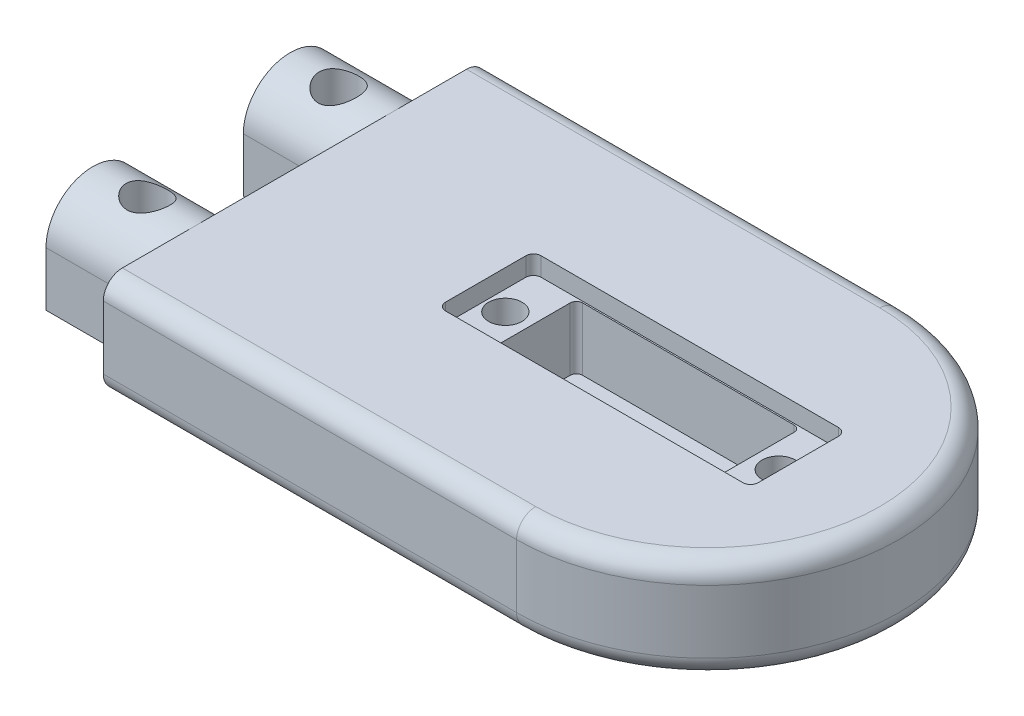
SolidWorks part; units mm, degrees
ref_plane "Front Plane" through (0, 0, 0) normal (0, 0, 1) x (1, 0, 0)
ref_plane "Top Plane" through (0, 0, 0) normal (0, 1, 0) x (1, 0, 0)
ref_plane "Right Plane" through (0, 0, 0) normal (1, 0, 0) x (0, 0, -1)
sketch "Sketch1" plane through (0, 0, 0) normal (1, 0, 0) x (0, 0, -1)
  line L0 (-20, -5.305) -> (20, -5.305)
  line L1 (-20, -5.305) -> (-20, 5.305)
  line L2 (-20, 5.305) -> (20, 5.305)
  line L3 (20, -5.305) -> (20, 5.305)
  line L4 (-20, 5.305) -> (20, -5.305) construction
  line L5 (-20, -5.305) -> (20, 5.305) construction
  point P5 (0, 0)
  dimension "D1" = 40
  dimension "D2" = 10.61
extrude "Boss-Extrude1" add sketch "Sketch1" along normal blind 63.235
sketch "Sketch2" plane through (0, 5.305, 0) normal (0, 1, 0) x (1, 0, 0)
  line L0 (63.235, -20) -> (63.235, 0)
  line L1 (63.235, 20) -> (63.235, -20) construction
  line L2 (63.235, -20) -> (43.235, -20)
  line L3 (63.235, -20) -> (0, -20) construction
  arc A0 (43.235, -20) -> (63.235, 0) centre (43.235, 0) ccw
extrude "Cut-Extrude1" cut sketch "Sketch2" against normal through all
ref_plane "Plane1" through (0, 0, 0) normal (0, 0, 1) x (1, 0, 0)
mirror "Mirror1" about plane through (0, 0, 0) normal (0, 0, 1) of "Cut-Extrude1"
sketch "Sketch3" plane through (0, 5.305, 0) normal (0, 1, 0) x (1, 0, 0)
  line L0 (20, 4.2) -> (20, -4.2)
  line L1 (51.91, 5) -> (41.54, 5)
  line L2 (52.71, -4.2) -> (52.71, 4.2)
  line L3 (41.54, -5) -> (51.91, -5)
  line L4 (31.17, -5) -> (41.54, -5)
  line L5 (41.54, 5) -> (31.17, 5)
  line L6 (31.17, 5) -> (20.8, 5)
  line L7 (20.8, -5) -> (31.17, -5)
  line L8 (43.235, 20) -> (0, 20) construction
  line L9 (0, 20) -> (0, -20) construction
  arc A0 (52.71, 4.2) -> (51.91, 5) centre (51.91, 4.2) ccw
  arc A1 (51.91, -5) -> (52.71, -4.2) centre (51.91, -4.2) ccw
  arc A2 (20.8, 5) -> (20, 4.2) centre (20.8, 4.2) ccw
  arc A3 (20, -4.2) -> (20.8, -5) centre (20.8, -4.2) ccw
  point P20 (20, 0)
  dimension "D4" = 0.8
  dimension "D1" = 20
  dimension "D2" = 32.71
  dimension "D3" = 10
extrude "Cut-Extrude2" cut sketch "Sketch3" against normal blind 1.95
sketch "Sketch4" plane through (0, 3.355, 0) normal (0, 1, 0) x (1, 0, 0)
  line L0 (48.07, -4.2) -> (48.07, 4.2)
  line L1 (47.42, 4.85) -> (25.29, 4.85)
  line L2 (25.29, -4.85) -> (47.42, -4.85)
  line L3 (24.64, 4.2) -> (24.64, -4.2)
  line L4 (20, 4.2) -> (20, -4.2) construction
  line L5 (51.91, 5) -> (20.8, 5) construction
  line L6 (20, 4.2) -> (20, -4.2) construction
  arc A0 (48.07, 4.2) -> (47.6946, 4.7891) centre (47.42, 4.2) ccw
  arc A1 (47.9885, -4.5151) -> (48.07, -4.2) centre (47.42, -4.2) ccw
  arc A2 (47.42, -4.85) -> (47.9885, -4.5151) centre (47.42, -4.2) ccw
  arc A3 (47.6946, 4.7891) -> (47.42, 4.85) centre (47.42, 4.2) ccw
  arc A4 (25.29, 4.85) -> (24.64, 4.2) centre (25.29, 4.2) ccw
  arc A5 (24.64, -4.2) -> (25.29, -4.85) centre (25.29, -4.2) ccw
  point P30 (20, 0)
  point P31 (24.64, 0)
  point P34 (36.355, 5)
  point P35 (36.355, -4.85)
  dimension "D1" = 0.65
  dimension "D2" = 9.7
  dimension "D3" = 23.43
  dimension "D4" = 27.6946
  dimension "D5" = 27.9885
extrude "Cut-Extrude3" cut sketch "Sketch4" against normal blind 6.56
sketch "Sketch5" plane through (0, -3.205, 0) normal (0, 1, 0) x (1, 0, 0)
  line L0 (47.42, 4.85) -> (25.29, 4.85) construction
  line L2 (48.07, -4.2) -> (48.07, 4.2) construction
  circle A0 centre (43.235, 0) radius 3.8
  dimension "D1" = 4.85
  dimension "D2" = 4.835
extrude "Cut-Extrude4" cut sketch "Sketch5" against normal through all
sketch "Sketch6" plane through (0, 3.355, 0) normal (0, 1, 0) x (1, 0, 0)
  line L7 (0, 0) -> (52.71, 0) construction
  line L8 (36.355, -5) -> (36.355, 5) construction
  line L15 (20.8, -5) -> (51.91, -5) construction
  line L16 (51.91, 5) -> (20.8, 5) construction
  line L17 (0, 20) -> (0, -20) construction
  line L18 (52.71, -4.2) -> (52.71, 4.2) construction
  circle A3 centre (50.655, 0) radius 1.75
  circle A4 centre (22.055, 0) radius 1.75
  point P29 (36.355, -5)
  point P33 (36.355, 5)
  point P37 (0, 0)
  point P42 (52.71, 0)
  dimension "D1" = 3.5
extrude "Cut-Extrude5" cut sketch "Sketch6" against normal blind 4.1
sketch "Sketch7" plane through (0, -0.745, 0) normal (0, 1, 0) x (1, 0, 0)
  line L0 (36.355, -5) -> (36.355, 5) construction
  line L1 (20.8, -5) -> (51.91, -5) construction
  circle A0 centre (50.655, 0) radius 1.125
  circle A2 centre (22.055, 0) radius 1.125
  circle A3 centre (50.655, 0) radius 1.75 construction
  dimension "D1" = 2.25
extrude "Cut-Extrude6" cut sketch "Sketch7" against normal blind 2
fillet "Fillet1" radius 2 6 edges at (21.6175, -5.305, -20) (63.235, -5.305, 0) (21.6175, 5.305, -20) (63.235, 5.305, 0) (21.6175, -5.305, 20) (21.6175, 5.305, 20)
sketch "Sketch8" plane through (0, 0, 0) normal (-1, 0, 0) x (0, 0, 1)
  line L0 (0, -5.305) -> (0, 5.305) construction
  line L5 (18, -5.305) -> (-18, -5.305) construction
  line L6 (-18, 5.305) -> (18, 5.305) construction
  line L7 (0, 0) -> (-20, 0) construction
  line L11 (-20, -3.305) -> (-20, 3.305) construction
  line L12 (-15.2212, 0.365) -> (-15.2212, -5.305)
  line L13 (-15.2212, -5.305) -> (-5.4212, -5.305)
  line L14 (-5.4212, -5.305) -> (-5.4212, 0.365)
  line L15 (-15.2212, -5.305) -> (-5.4212, 5.305) construction
  line L16 (-5.4212, -5.305) -> (-15.2212, 5.305) construction
  line L17 (15.2212, 0.365) -> (15.2212, -5.305)
  line L18 (15.2212, -5.305) -> (5.4212, -5.305)
  line L19 (5.4212, -5.305) -> (5.4212, 0.365)
  arc A2 (-15.2212, 0.365) -> (-5.4212, 0.365) centre (-10.3212, 0.365) cw
  arc A3 (15.2212, 0.365) -> (5.4212, 0.365) centre (10.3212, 0.365) ccw
  point P20 (-10.3212, 0)
  dimension "D1" = 9.8
  dimension "D2" = 0.365
  dimension "D3" = 9.6788
extrude "Boss-Extrude2" add sketch "Sketch8" along normal blind 10.77
sketch "Sketch9" plane through (0, -5.305, 0) normal (0, -1, 0) x (1, 0, 0)
  line L0 (-10.77, 15.2212) -> (0, 15.2212) construction
  line L2 (0, 0) -> (-10.77, 0) construction
  line L4 (0.0002, -37.2792) -> (0.0002, 37.2792) construction
  circle A0 centre (-5.385, 10) radius 2.125
  circle A1 centre (-5.385, -10) radius 2.125
  dimension "D1" = 4.25
  dimension "D2" = 5.2212
  dimension "D3" = 5.3852
extrude "Cut-Extrude7" cut sketch "Sketch9" against normal through all
